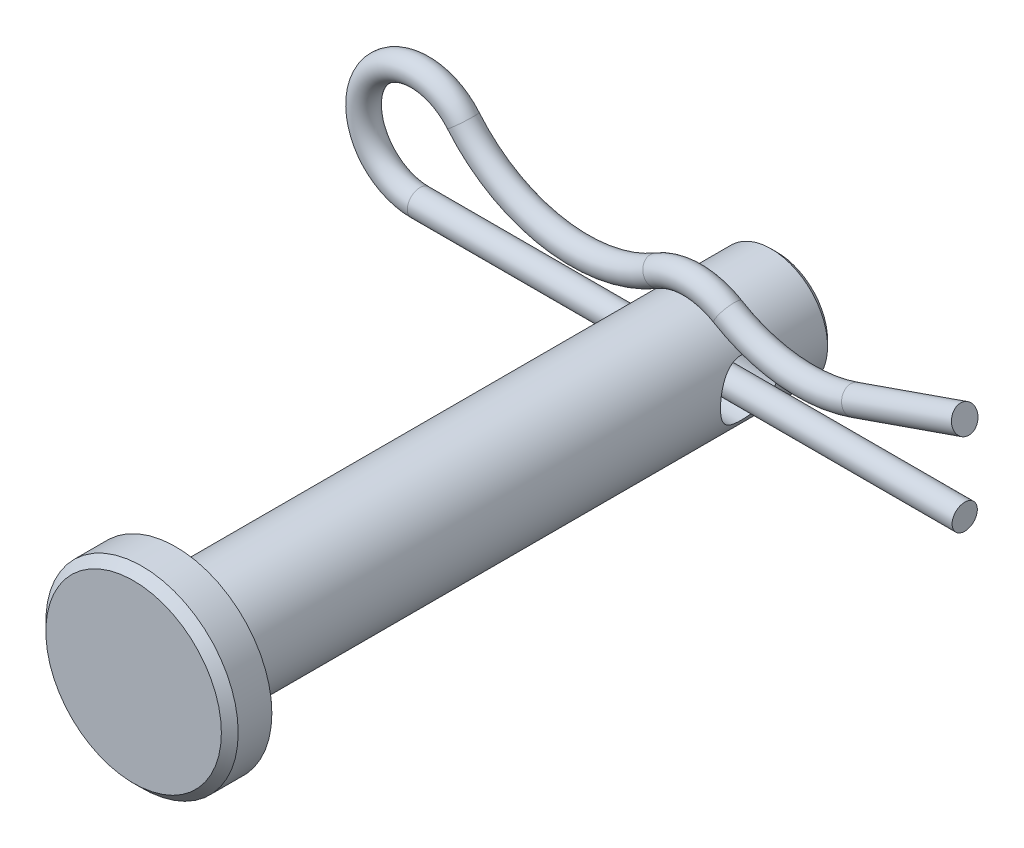
SolidWorks part; units mm, degrees
material "Plain Carbon Steel"
ref_plane "Front" through (0, 0, 0) normal (0, 0, 1) x (1, 0, 0)
ref_plane "Top" through (0, 0, 0) normal (0, 1, 0) x (1, 0, 0)
ref_plane "Right" through (0, 0, 0) normal (1, 0, 0) x (0, 0, -1)
sketch "Sketch1" plane through (0, 0, 0) normal (0, 0, 1) x (1, 0, 0)
  circle A0 centre (0, 0) radius 2.3813
  point P3 (0, 2.3813)
  point P4 (0, -2.3813)
  dimension "dia" = 4.7625
extrude "Extrude1" add sketch "Sketch1" along normal mid plane 25.4
sketch "Sketch2" plane through (0, 0, 12.7) normal (0, 0, 1) x (1, 0, 0)
  circle A0 centre (0, 0) radius 4.064
  dimension "head dia" = 8.128
extrude "Extrude2" add sketch "Sketch2" along normal blind 1.778
chamfer "Chamfer1" distance 0.3556 angle 45 1 edges at (4.064, 0, 14.478)
sketch "Sketch3" plane through (0, 0, 0) normal (1, 0, 0) x (0, 0, -1)
  line L0 (-12.7, -2.3813) -> (-12.7, 2.3813) construction
  circle A0 centre (9.1281, 0) radius 1.1906
  point P2 (7.9375, 0)
  dimension "hole dia" = 2.3813
  dimension "useable Lg" = 20.6375
extrude "Extrude3" cut sketch "Sketch3" against normal through all and the other way through all
chamfer "Chamfer2" distance 0.2381 angle 45 1 edges at (2.3813, 0, -12.7)
ref_plane "Plane1" through (0, 0, -9.1281) normal (0, 0, 1) x (1, 0, 0)
sketch "Sketch6" plane through (0, 0, -9.1281) normal (0, 0, 1) x (1, 0, 0)
  line L0 (11.5094, 0) -> (-11.5094, 0)
  line L1 (6.8677, 1.9555) -> (11.5094, 3.5719)
  line L2 (-11.5094, 2.3813) -> (-11.5094, 4.7625) construction
  arc A0 (-11.5094, 0) -> (-9.6784, 3.9037) centre (-11.5094, 2.3813) cw
  arc A1 (1.4937, 2.5028) -> (-1.4937, 2.5028) centre (0, 0) ccw
  circle A2 centre (0, 0) radius 0.5334 construction
  arc A3 (-1.4937, 2.5028) -> (-9.6784, 3.9037) centre (-4.7672, 7.9875) cw
  circle A4 centre (0, 2.9147) radius 0.5334 construction
  circle A5 centre (0, 0) radius 2.3813 construction
  arc A6 (1.4937, 2.5028) -> (6.8677, 1.9555) centre (4.7672, 7.9875) ccw
  point P2 (-4.7672, 1.6002)
  point P9 (-11.5094, 3.5719)
  point P18 (-13.8906, 2.3813)
  point P22 (-11.5094, 4.7625)
  point P23 (0, 0.5334)
  dimension "pin dia" = 1.0668
  dimension "D2" = 4.7625
  dimension "pin Lg" = 25.4
  dimension "D1" = 1.6002
ref_plane "Plane2" through (11.5094, 0, -9.1281) normal (-1, 0, 0) x (0, 0, 1)
sketch "Sketch7" plane through (11.5094, 0, -9.1281) normal (-1, 0, 0) x (0, 0, 1)
  circle A0 centre (0, 0) radius 0.5334
sweep "Sweep1" add profiles "Sketch7" path "Sketch6"
sketch "Sketch8" plane through (0, 0, 0) normal (1, 0, 0) x (0, 0, -1)
  line L0 (-14.478, 3.7084) -> (-14.478, -3.7084) construction
  line L1 (-14.1224, -4.064) -> (-12.7, -4.064) construction
  line L2 (12.7, -2.1431) -> (12.7, 2.1431) construction
  line L3 (7.9375, 5.2959) -> (9.1281, 5.2959) construction
  line L4 (9.1281, 2.3813) -> (9.1281, 4.7625) construction
  arc A0 (9.6615, 4.7625) -> (8.5947, 4.7625) centre (9.1281, 4.7625) ccw construction
  point P0 (-14.478, 4.064)
  point P1 (-12.7, 4.064)
  point P5 (12.7, 2.3813)
  point P8 (-14.478, -4.064)
  point P9 (12.7, -2.3813)
  point P12 (7.9375, 5.2959)
equation "\"D1@Chamfer1\" = \"head ht@Extrude2\" * .2"
equation "\"D1@Chamfer2\" = \"dia@Sketch1\" * .05"
equation "\"D2@Sketch6\" = \"dia@Sketch1\" * 1"
equation "\"D1@Sketch6\" = \"pin dia@Sketch6\" * 1.5"
